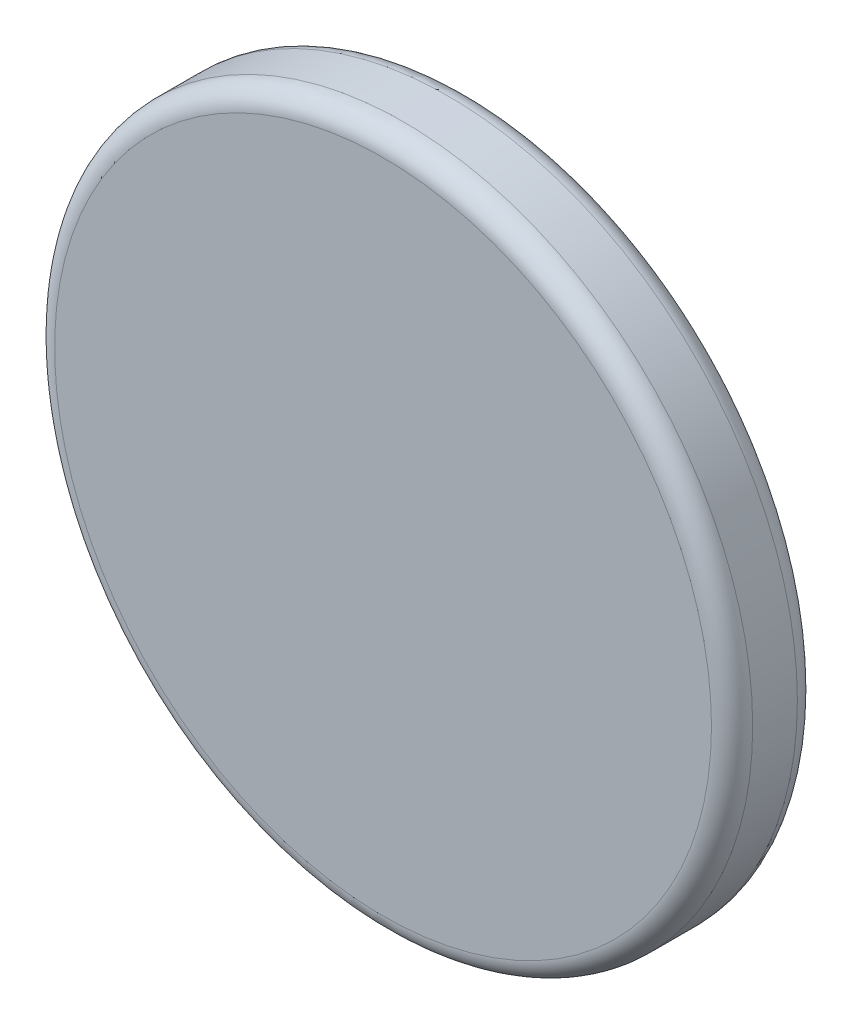
SolidWorks part; units mm, degrees
material "Rubber"
ref_plane "Front Plane" through (0, 0, 0) normal (0, 0, 1) x (1, 0, 0)
ref_plane "Top Plane" through (0, 0, 0) normal (0, 1, 0) x (1, 0, 0)
ref_plane "Right Plane" through (0, 0, 0) normal (1, 0, 0) x (0, 0, -1)
sketch "Sketch1" plane through (0, 0, 0) normal (0, 0, 1) x (1, 0, 0)
  circle A0 centre (0, 0) radius 203.2
  dimension "D1" = 406.4
extrude "Boss-Extrude1" add sketch "Sketch1" along normal mid plane 50
fillet "Fillet1" radius 12 2 edges at (203.2, 0, -25) (203.2, 0, 25)
equation "\"tire_diameter\"= 16in"
equation "\"tire_width\" = 50mm"
equation "\"D1@Boss-Extrude1\"=\"tire_width\""
